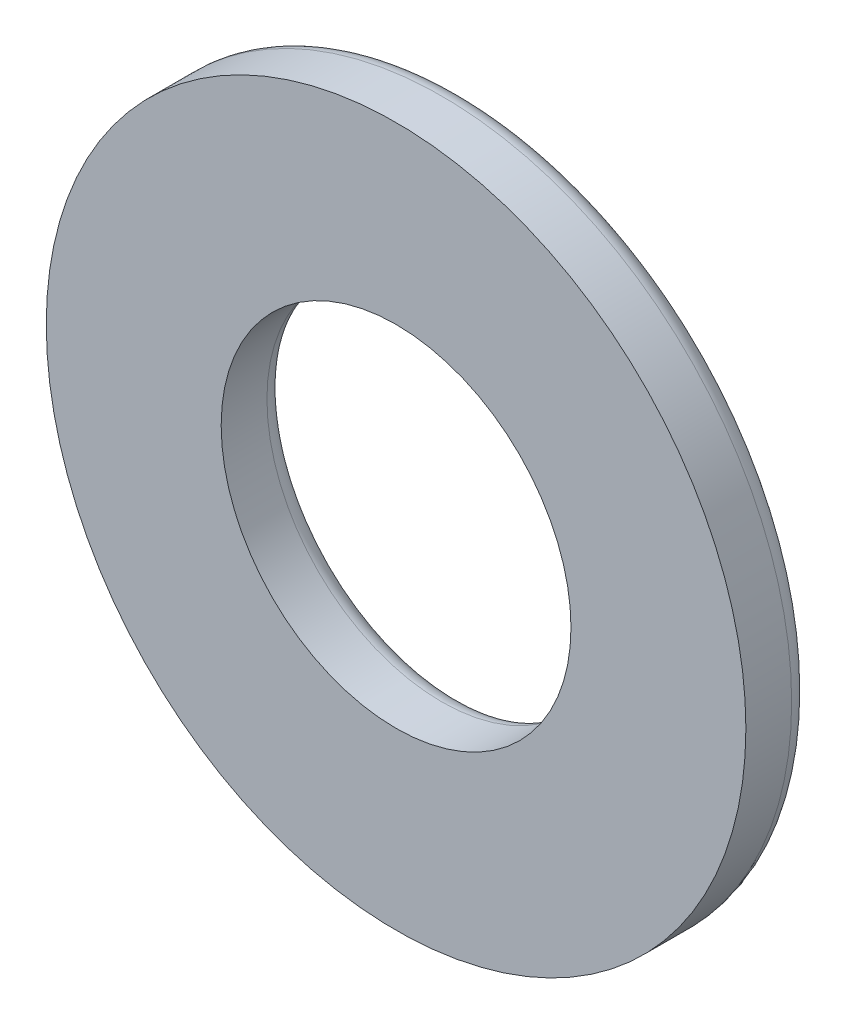
SolidWorks part; units mm, degrees
material "Stainless Steel (ferritic)"
ref_plane "Front Plane" through (0, 0, 0) normal (0, 0, 1) x (1, 0, 0)
ref_plane "Top Plane" through (0, 0, 0) normal (0, 1, 0) x (1, 0, 0)
ref_plane "Right Plane" through (0, 0, 0) normal (1, 0, 0) x (0, 0, -1)
sketch "Sketch1" plane through (0, 0, 0) normal (0, 0, 1) x (1, 0, 0)
  circle A0 centre (0, 0) radius 6.7945
  circle A1 centre (0, 0) radius 13.589
  dimension "D1" = 27.178
  dimension "D2" = 13.589
extrude "Boss-Extrude1" add sketch "Sketch1" along normal blind 2.54
fillet "Fillet1" radius 0.762 2 edges at (6.7945, 0, 0) (13.589, 0, 0)
